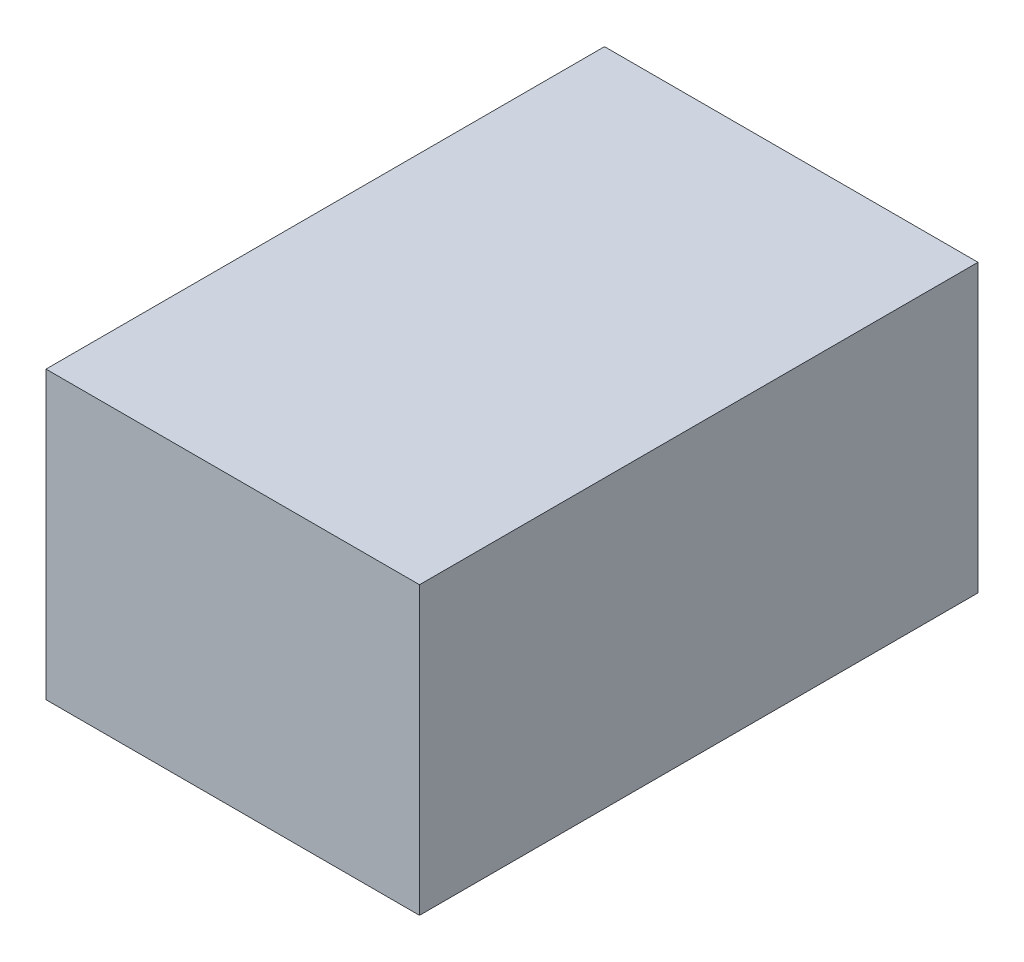
SolidWorks part; units mm, degrees
ref_plane "Front Plane" through (0, 0, 0) normal (0, 0, 1) x (1, 0, 0)
ref_plane "Top Plane" through (0, 0, 0) normal (0, 1, 0) x (1, 0, 0)
ref_plane "Right Plane" through (0, 0, 0) normal (1, 0, 0) x (0, 0, -1)
sketch "Sketch1" plane through (0, 0, 0) normal (0, 0, 1) x (1, 0, 0)
  line L1 (22.8, -17.6367) -> (-7.2, -17.6367)
  line L2 (22.8, -17.6367) -> (22.8, -40.6367)
  line L3 (22.8, -40.6367) -> (-7.2, -40.6367)
  line L4 (-7.2, -17.6367) -> (-7.2, -40.6367)
  dimension "D1" = 30
  dimension "D2" = 23
extrude "Boss-Extrude1" add sketch "Sketch1" along normal blind 44.86
